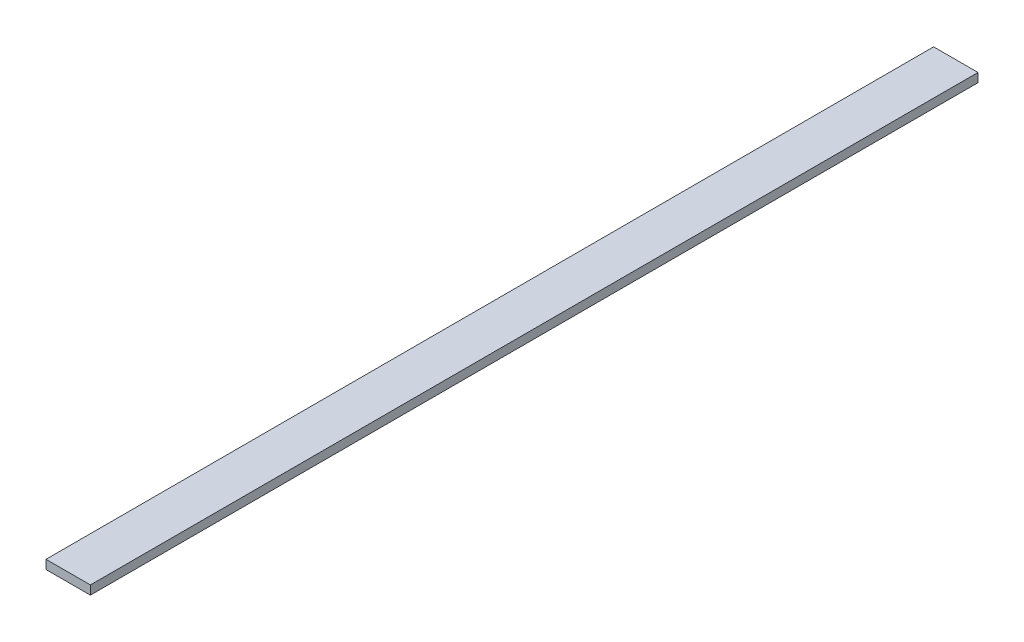
SolidWorks part; units mm, degrees
ref_plane "前视基准面" through (0, 0, 0) normal (0, 0, 1) x (1, 0, 0)
ref_plane "上视基准面" through (0, 0, 0) normal (0, 1, 0) x (1, 0, 0)
ref_plane "右视基准面" through (0, 0, 0) normal (1, 0, 0) x (0, 0, -1)
sketch "草图1" plane through (0, 0, 0) normal (0, 0, 1) x (1, 0, 0)
  line L1 (-50, -10) -> (50, -10)
  line L2 (-50, -10) -> (-50, 10)
  line L3 (-50, 10) -> (50, 10)
  line L4 (50, -10) -> (50, 10)
  line L5 (-50, -10) -> (50, 10) construction
  line L6 (-50, 10) -> (50, -10) construction
  point P0 (0, 0)
  dimension "D1" = 100
  dimension "D2" = 20
extrude "凸台-拉伸1" add sketch "草图1" along normal blind 2000
